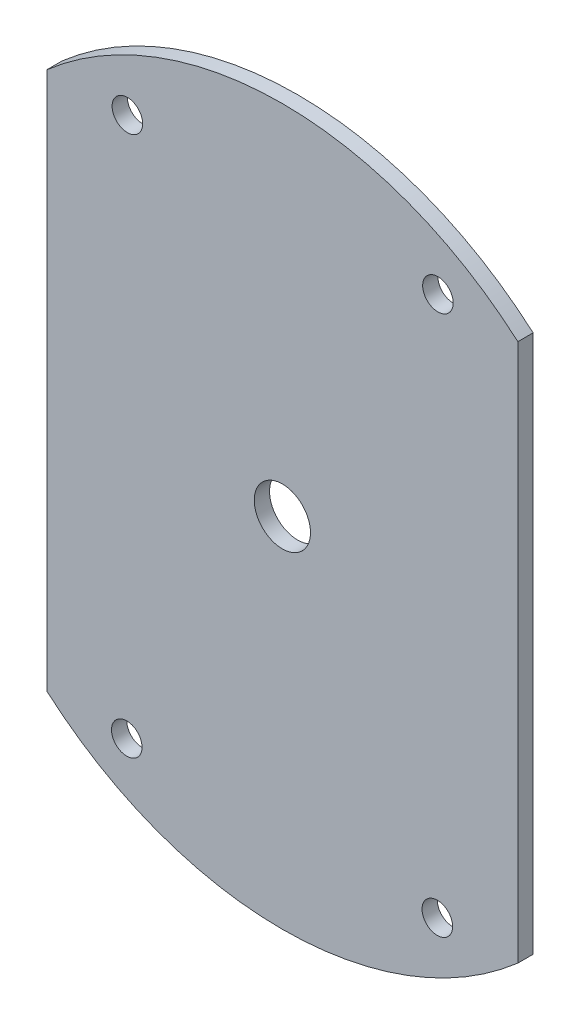
SolidWorks part; units mm, degrees
ref_plane "Front Plane" through (0, 0, 0) normal (0, 0, 1) x (1, 0, 0)
ref_plane "Top Plane" through (0, 0, 0) normal (0, 1, 0) x (1, 0, 0)
ref_plane "Right Plane" through (0, 0, 0) normal (1, 0, 0) x (0, 0, -1)
sketch "Sketch3" plane through (0, 0, 0) normal (0, 0, 1) x (1, 0, 0)
  line L0 (-32.1982, 56.1283) -> (32.1982, -56.1283) construction
  line L1 (32.1982, -56.1283) -> (32.3227, 56.1283) construction
  line L2 (32.3227, 56.1283) -> (-32.3227, -56.1283) construction
  line L3 (32.3227, 56.1283) -> (-32.1982, 56.1283) construction
  line L4 (-32.1982, 56.1283) -> (-32.3227, -56.1283) construction
  line L5 (-32.3227, -56.1283) -> (32.1982, -56.1283) construction
  circle A0 centre (0, 0) radius 74.295
  circle A1 centre (-32.1982, 56.1283) radius 3.175
  circle A2 centre (32.3227, 56.1283) radius 3.175
  circle A3 centre (-32.3227, -56.1283) radius 3.175
  circle A4 centre (32.1982, -56.1283) radius 3.175
  circle A5 centre (0, 0) radius 5.842
  dimension "D3" = 6.35
  dimension "D4" = 148.59
  dimension "D5" = 11.684
  dimension "D1" = 112.2566
  dimension "D2" = 64.521
extrude "Boss-Extrude2" add sketch "Sketch3" along normal blind 3.175 contours A0
sketch "Sketch4" plane through (0, 0, 3.175) normal (0, 0, 1) x (1, 0, 0)
  line L0 (-48.9302, 55.9069) -> (-48.9302, -55.9069)
  line L1 (0, 74.295) -> (0, -74.295) construction
  line L2 (48.9302, 55.9069) -> (48.9302, -55.9069)
  circle A0 centre (0, 0) radius 74.295 construction
  arc A1 (-48.9302, 55.9069) -> (-48.9302, -55.9069) centre (0, 0) ccw
  arc A2 (48.9302, 55.9069) -> (48.9302, -55.9069) centre (0, 0) cw
extrude "Cut-Extrude2" cut sketch "Sketch4" against normal through all
